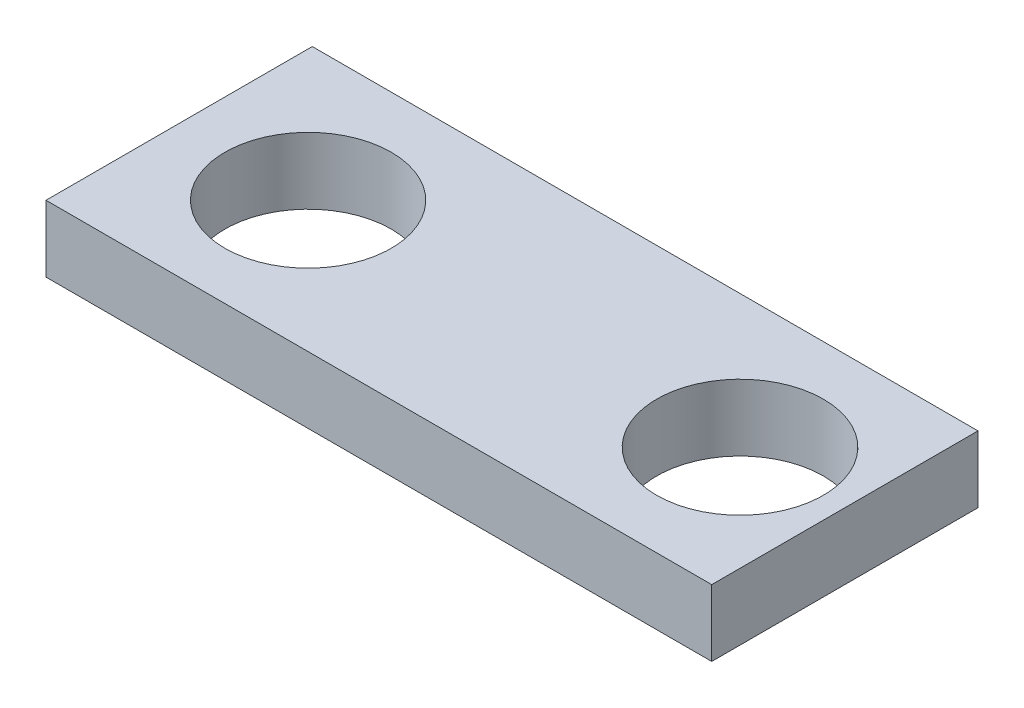
SolidWorks part; units mm, degrees
ref_plane "Front Plane" through (0, 0, 0) normal (0, 0, 1) x (1, 0, 0)
ref_plane "Top Plane" through (0, 0, 0) normal (0, 1, 0) x (1, 0, 0)
ref_plane "Right Plane" through (0, 0, 0) normal (1, 0, 0) x (0, 0, -1)
sketch "Sketch1" plane through (0, 0, 0) normal (0, 1, 0) x (1, 0, 0)
  line L1 (0, 0) -> (127, 0)
  line L2 (0, 0) -> (0, 50.8)
  line L3 (0, 50.8) -> (127, 50.8)
  line L4 (127, 0) -> (127, 50.8)
  dimension "D1" = 127
  dimension "D2" = 50.8
extrude "Boss-Extrude1" add sketch "Sketch1" along normal blind 12.7
sketch "Sketch2" plane through (0, 12.7, 0) normal (0, 1, 0) x (1, 0, 0)
  line L1 (0, 0) -> (25, 0)
  line L2 (0, 0) -> (0, 25)
  line L3 (0, 25) -> (25, 25)
  line L4 (25, 0) -> (25, 25)
  circle A0 centre (25, 25) radius 15.875
  dimension "D1" = 25
  dimension "D2" = 25
extrude "Cut-Extrude1" cut sketch "Sketch2" against normal blind 12.7 contours L4 A0 L3 | L3 A0 L4
sketch "Sketch4" plane through (0, 12.7, 0) normal (0, 1, 0) x (1, 0, 0)
  line L1 (0, 0) -> (107, 0)
  line L2 (0, 0) -> (0, 25.4)
  line L3 (0, 25.4) -> (107, 25.4)
  line L4 (107, 0) -> (107, 25.4)
  circle A0 centre (107, 25.4) radius 15.9
  dimension "D1" = 25.4
  dimension "D2" = 107
extrude "Cut-Extrude2" cut sketch "Sketch4" against normal through all contours L4 A0 L3 | L3 A0 L4
